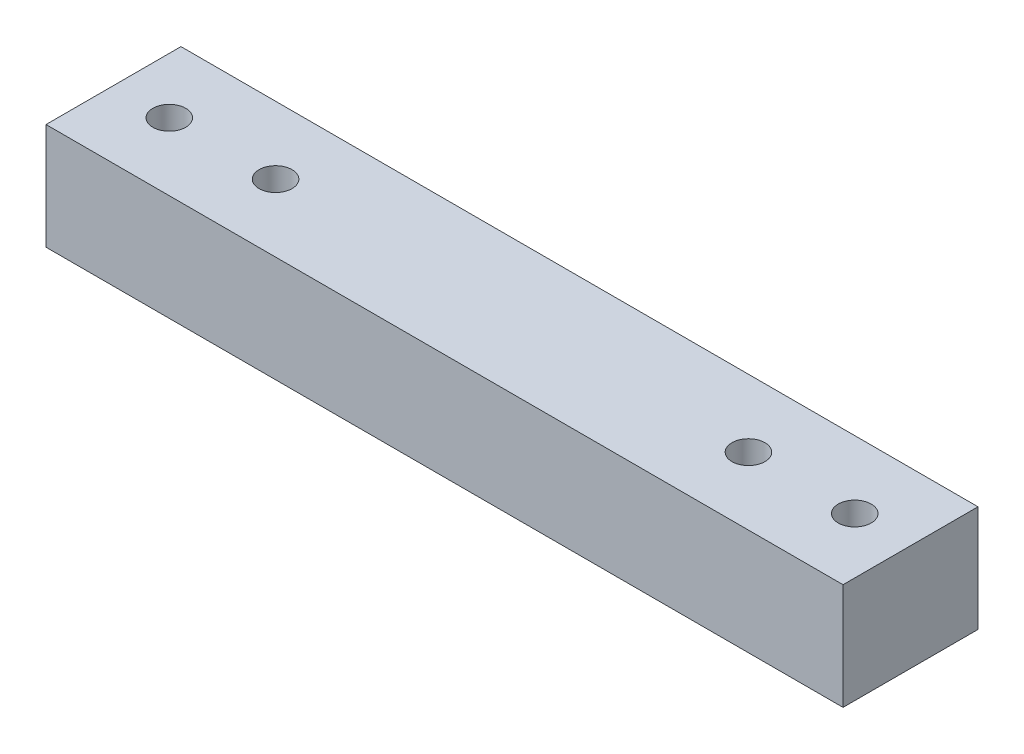
SolidWorks part; units mm, degrees
ref_plane "Front Plane" through (0, 0, 0) normal (0, 0, 1) x (1, 0, 0)
ref_plane "Top Plane" through (0, 0, 0) normal (0, 1, 0) x (1, 0, 0)
ref_plane "Right Plane" through (0, 0, 0) normal (1, 0, 0) x (0, 0, -1)
sketch "Sketch1" plane through (0, 0, 0) normal (0, 1, 0) x (1, 0, 0)
  line L1 (-37.5, -6.35) -> (37.5, -6.35)
  line L2 (-37.5, -6.35) -> (-37.5, 6.35)
  line L3 (-37.5, 6.35) -> (37.5, 6.35)
  line L4 (37.5, -6.35) -> (37.5, 6.35)
  line L5 (-37.5, -6.35) -> (37.5, 6.35) construction
  line L6 (-37.5, 6.35) -> (37.5, -6.35) construction
  point P0 (0, 0)
  dimension "D1" = 12.7
  dimension "D2" = 75
extrude "Boss-Extrude1" add sketch "Sketch1" along normal blind 10
sketch "Sketch2" plane through (0, 10, 0) normal (0, 1, 0) x (1, 0, 0)
  line L0 (37.5, -6.35) -> (37.5, 6.35) construction
  line L1 (0, -5.5) -> (0, 5.5) construction
  circle A0 centre (32.25, 0) radius 1.55
  circle A1 centre (22.25, 0) radius 1.55
  circle A2 centre (-32.25, 0) radius 1.55
  circle A3 centre (-22.25, 0) radius 1.55
  dimension "D3" = 3.1
  dimension "D1" = 3.7
  dimension "D2" = 13.7
extrude "Cut-Extrude1" cut sketch "Sketch2" against normal through all
